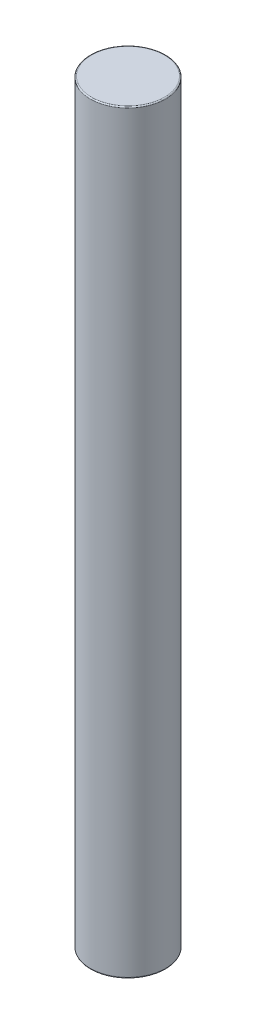
SolidWorks part; units mm, degrees
ref_plane "Front Plane" through (0, 0, 0) normal (0, 0, 1) x (1, 0, 0)
ref_plane "Top Plane" through (0, 0, 0) normal (0, 1, 0) x (1, 0, 0)
ref_plane "Right Plane" through (0, 0, 0) normal (1, 0, 0) x (0, 0, -1)
sketch "Sketch1" plane through (0, 0, 0) normal (0, 1, 0) x (1, 0, 0)
  circle A0 centre (0, 0) radius 1.6
  dimension "D1" = 3.2
extrude "Extrude1" add sketch "Sketch1" along normal blind 32.1
fillet "Fillet1" radius 0.05 2 edges at (0, 0, 1.6) (0, 32.1, 1.6)
